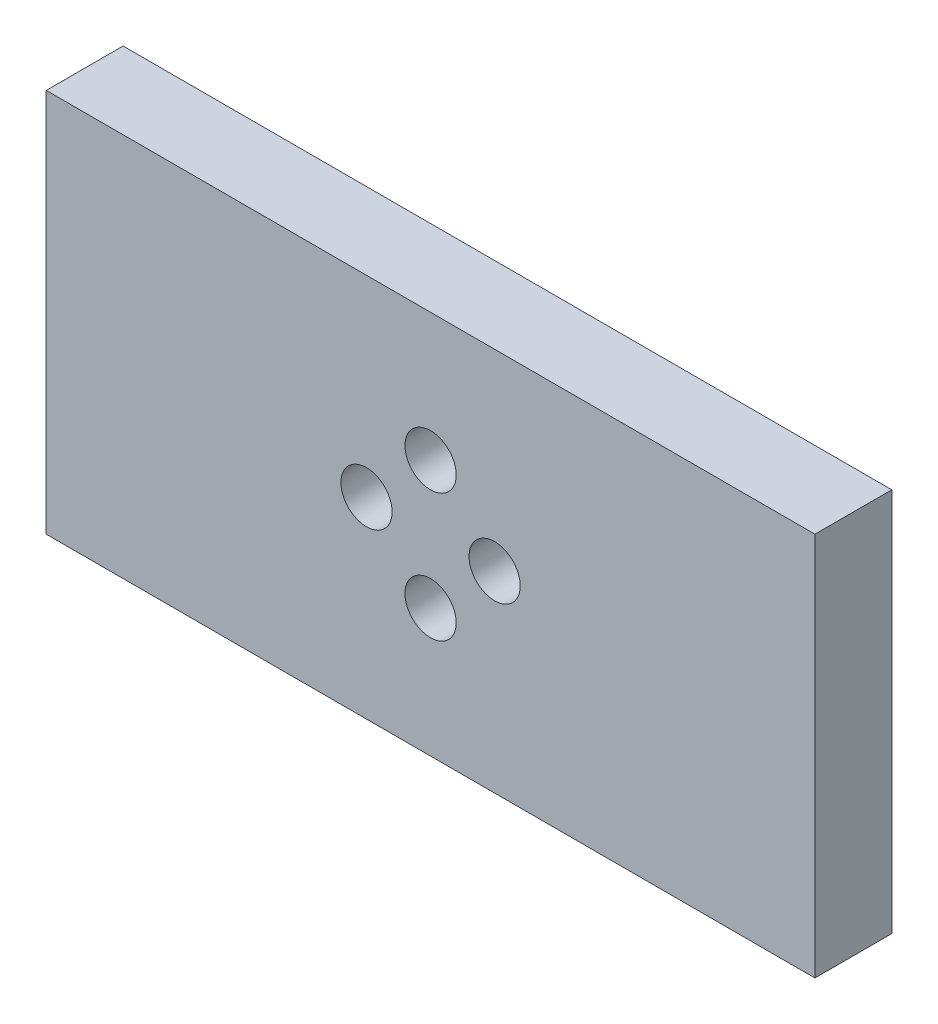
SolidWorks part; units mm, degrees
material "Cedar"
ref_plane "Front Plane" through (0, 0, 0) normal (0, 0, 1) x (1, 0, 0)
ref_plane "Top Plane" through (0, 0, 0) normal (0, 1, 0) x (1, 0, 0)
ref_plane "Right Plane" through (0, 0, 0) normal (1, 0, 0) x (0, 0, -1)
sketch "Sketch1" plane through (0, 0, 0) normal (0, 0, 1) x (1, 0, 0)
  line L1 (-15, -7.5) -> (15, -7.5)
  line L2 (-15, -7.5) -> (-15, 7.5)
  line L3 (-15, 7.5) -> (15, 7.5)
  line L4 (15, -7.5) -> (15, 7.5)
  line L5 (-15, -7.5) -> (15, 7.5) construction
  line L6 (-15, 7.5) -> (15, -7.5) construction
  point P0 (0, 0)
  dimension "D1" = 30
  dimension "D2" = 15
extrude "Boss-Extrude1" add sketch "Sketch1" along normal blind 3
sketch "Sketch2" plane through (0, 0, 3) normal (0, 0, 1) x (1, 0, 0)
  circle A0 centre (0, 2.5) radius 1
  circle A1 centre (2.5, 0) radius 1
  circle A2 centre (0, -2.5) radius 1
  circle A3 centre (-2.5, 0) radius 1
  point P12 (0, 0)
  dimension "D1" = 2.5
  dimension "D2" = 4
extrude "Cut-Extrude1" cut sketch "Sketch2" against normal blind 10
